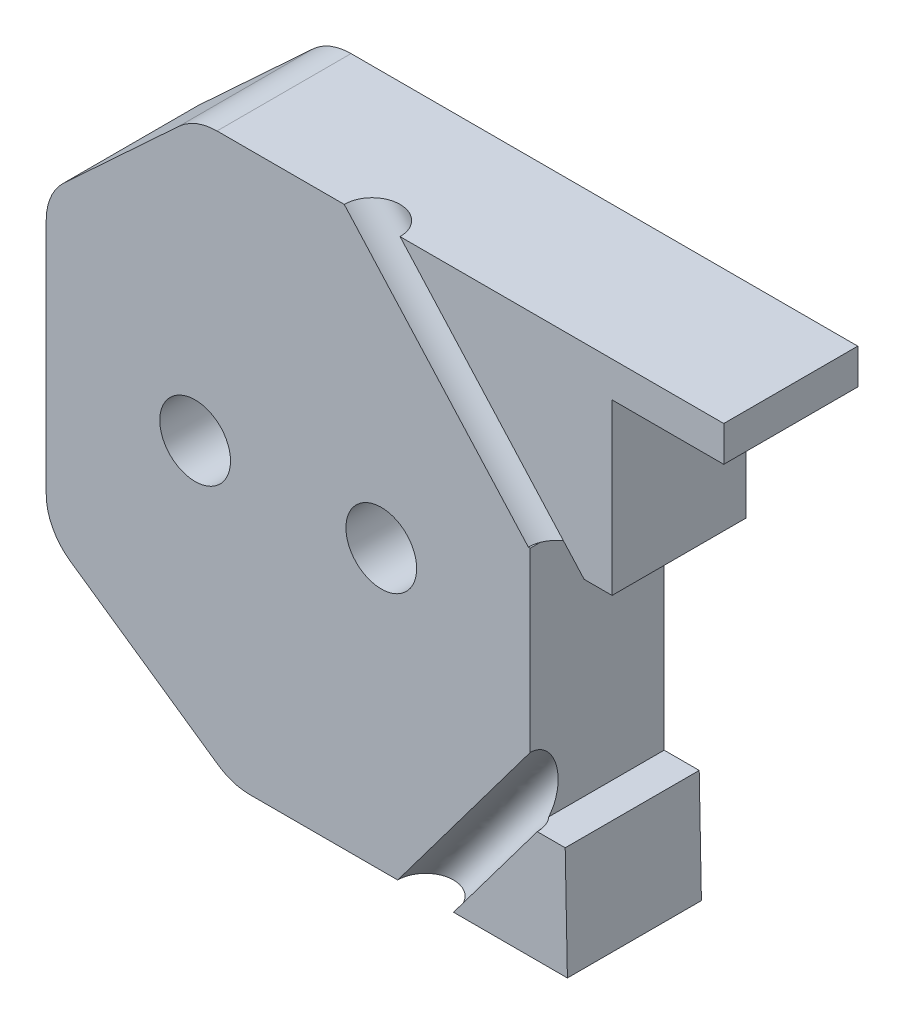
SolidWorks part; units mm, degrees
ref_plane "Front Plane" through (0, 0, 0) normal (0, 0, 1) x (1, 0, 0)
ref_plane "Top Plane" through (0, 0, 0) normal (0, 1, 0) x (1, 0, 0)
ref_plane "Right Plane" through (0, 0, 0) normal (1, 0, 0) x (0, 0, -1)
sketch "Sketch2" plane through (0, 0, 0) normal (0, 0, 1) x (1, 0, 0)
  line L1 (-2.5, 7.5) -> (-16.7, 7.5)
  line L2 (-20.7, 3.7934) -> (-20.7, -4.0316)
  line L3 (-15.7, -7.5) -> (-6.7, -7.5)
  line L4 (-6.7, -7.5) -> (-4.2, -5.6)
  line L5 (-2.5, 7.5) -> (0, 7.5)
  line L7 (0, 7) -> (0, 7.5)
  line L8 (-20.7, 3.7934) -> (-16.7, 7.5)
  line L9 (-20.7, -4.0316) -> (-15.7, -7.5)
  arc A1 (-4.2, -5.6) -> (7, 0) centre (0, 0) ccw
  arc A2 (7, 0) -> (0, 7) centre (0, 0) ccw
  dimension "D1" = 7
  dimension "D2" = 4
  dimension "D3" = 5
  dimension "D4" = 7.5
  dimension "D5" = 15
  dimension "D7" = 2.5
  dimension "D8" = 14
extrude "Boss-Extrude1" add sketch "Sketch2" along normal blind 2 contours A1 A2 L7 L5 L1 L8 L2 L9 L3 L4
sketch "Sketch4" plane through (0, 0, 2) normal (0, 0, 1) x (1, 0, 0)
  line L7 (-15.7, -7.5) -> (-6.7, -7.5)
  line L8 (-6.7, -7.5) -> (-6.7591, -4.5)
  line L9 (-6.7591, -4.5) -> (-7.7, -4.5)
  line L10 (-16.7, 7.5) -> (-2.5, 7.5)
  line L13 (-5.5, 2) -> (-5.5, 5.3)
  line L14 (-5.5, 5.3) -> (-2.5, 5.3)
  line L21 (-20.7, -4.0316) -> (-15.7, -7.5)
  line L24 (-16.7, 7.5) -> (-20.7, 3.7934)
  line L25 (-20.7, -4.0316) -> (-20.7, 3.7934)
  line L26 (-7.7, 2) -> (-5.5, 2)
  line L29 (-7.7, 2) -> (-7.7, -4.5)
  line L30 (-2.5, 7.5) -> (-2.5, 5.3)
  point P2 (-5.5, 3.65)
  dimension "D1" = 13
  dimension "D2" = 2.5
  dimension "D3" = 3
  dimension "D4" = 3
extrude "Boss-Extrude2" add sketch "Sketch4" along normal blind 6
ref_point "Point1"
sketch "Sketch22" plane through (0, 0, 2) normal (0, 0, 1) x (1, 0, 0)
  line L0 (0, 5.3) -> (-14, 5.3) construction
  line L1 (0, 4) -> (-14, 4) construction
  line L2 (-14, 4) -> (-14, 5.3) construction
  circle A0 centre (0, 0) radius 5.3 construction
  circle A1 centre (0, 0) radius 4 construction
  dimension "D1" = 14
  dimension "D2" = 10.6
  dimension "D3" = 8
sketch "Sketch24" plane through (0, 0, 2) normal (0, 0, 1) x (1, 0, 0)
  circle A0 centre (0, 0) radius 3.9
  dimension "D1" = 7.8
extrude "Boss-Extrude5" add sketch "Sketch24" along normal blind 2.3
sketch "Sketch29" plane through (-5.5, 0, 0) normal (1, 0, 0) x (0, 0, -1)
  line L0 (-1.9279, 3.9758) -> (-8, 3.9758) construction
  line L1 (-8, 2) -> (-8, 5.3) construction
sketch "Sketch30" plane through (-5.5, 0, 0) normal (1, 0, 0) x (0, 0, -1)
  line L0 (-4.4659, 3.9758) -> (-4.4659, 5.3)
  line L1 (-4.4659, 3.9758) -> (-2.0573, 3.9758)
  line L2 (-4.4659, 5.3) -> (-2.0573, 5.3)
  line L3 (-2.0573, 3.9758) -> (-2.0573, 5.3)
  line L4 (-1.9279, 3.9758) -> (-8, 3.9758) construction
  line L5 (-8, 5.3) -> (-2, 5.3) construction
extrude "Cut-Extrude12" cut sketch "Sketch30" against normal blind 8
ref_plane "Plane1" through (0, 0, 8) normal (0, 0, 1) x (1, 0, 0)
sketch "Sketch8" plane through (0, 0, 2) normal (0, 0, 1) x (1, 0, 0)
  circle A1 centre (0, 0) radius 3.8
  circle A2 centre (0, 0) radius 2.5
sketch "Sketch28" plane through (0, 0, 4.3) normal (0, 0, 1) x (1, 0, 0)
  line L0 (-1, 1.7321) -> (-1, -1.7321)
  arc A0 (-1, -1.7321) -> (-1, 1.7321) centre (0, 0) ccw
  dimension "D1" = 1
  dimension "D2" = 2
extrude "Cut-Extrude11" cut sketch "Sketch28" against normal through all
sketch "Sketch33" plane through (0, 0, 8) normal (0, 0, 1) x (1, 0, 0)
  line L0 (-7, 2) -> (-0.5657, -5.1566) construction
  line L2 (-8.2591, -4.5) -> (-2.6001, 3.0469) construction
  point P2 (0, 0)
  point P8 (0, 0)
  dimension "D1" = 1.5
  dimension "D2" = 1.5
fillet "Fillet1" radius 1.5 9 edges at (-11.2, -7.5, 0) (-8.35, 7.5, 0) (-18.7, 5.6467, 0) (-18.2, -5.7658, 0) (-20.7, -0.1191, 0) (-15.7, -7.5, 4) (-20.7, -4.0316, 4) (-20.7, 3.7934, 4) (-16.7, 7.5, 4)
sketch "Sketch34" plane through (0, 2, 0) normal (0, -1, 0) x (1, 0, 0)
  line L0 (-5.5, 1.9279) -> (-5.5, 8) construction
  circle A0 centre (-7, 8) radius 0.75
  point P3 (0, 0)
  dimension "D1" = 1.5
  dimension "D2" = 1.5
extrude "Cut-Extrude13" cut sketch "Sketch34" along direction (0.6686, -0.7436, 0) on the side against the normal blind 8
sketch "Sketch35" plane through (0, -4.5, 0) normal (0, 1, 0) x (1, 0, 0)
  circle A0 centre (-8.2591, -8) radius 0.75
extrude "Cut-Extrude14" cut sketch "Sketch35" along direction (0.5999, 0.8001, 0) on the side against the normal blind 8 and the other way blind 3
sketch "Sketch36" plane through (0, 0, 8) normal (0, 0, 1) x (1, 0, 0)
  line L2 (-7.7, -2.7542) -> (-7.7, 2) construction
  circle A0 centre (-11.7, 0) radius 0.95
  circle A1 centre (-16.7, 0) radius 0.95
  dimension "D1" = 4
  dimension "D2" = 5
extrude "Cut-Extrude15" cut sketch "Sketch36" against normal blind 8
sketch "Sketch37" plane through (0, 0, 0) normal (0, 0, -1) x (-1, 0, 0)
  circle A0 centre (11.7, 0) radius 2
  circle A1 centre (16.7, 0) radius 2
extrude "Cut-Extrude16" cut sketch "Sketch37" against normal blind 2.5
sketch "Sketch38" plane through (0, 0, 8) normal (0, 0, 1) x (1, 0, 0)
  line L0 (-5.5, 5.3) -> (-2.5, 5.3)
  line L1 (-5.5, 5.3) -> (-5.5, 6.55)
  line L2 (-2.5, 5.3) -> (-2.5, 6.55)
  line L3 (-5.5, 6.55) -> (-2.5, 6.55)
  dimension "D1" = 1.25
extrude "Cut-Extrude17" cut sketch "Sketch38" against normal blind 3.6
ref_plane "Plane2" through (0, 0, 4.4) normal (0, 0, 1) x (1, 0, 0)
split "Split1" trim tools "Plane2" bodies to split 129 resulting bodies 130 131
delete or keep bodies "Body-Delete/Keep 1" type delete bodies bodies 131
